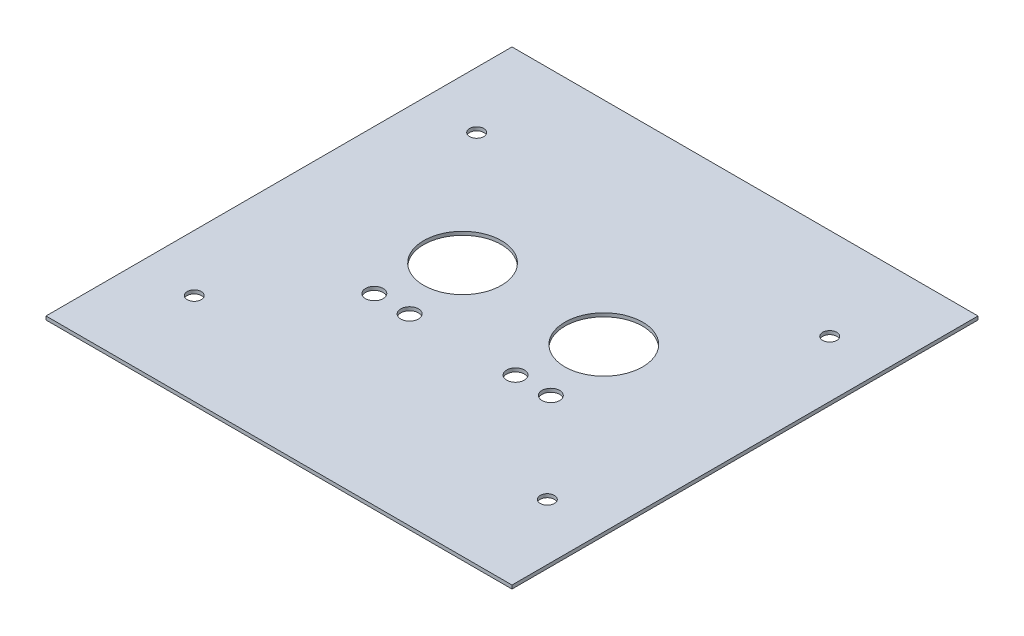
SolidWorks part; units mm, degrees
ref_plane "Front Plane" through (0, 0, 0) normal (0, 0, 1) x (1, 0, 0)
ref_plane "Top Plane" through (0, 0, 0) normal (0, 1, 0) x (1, 0, 0)
ref_plane "Right Plane" through (0, 0, 0) normal (1, 0, 0) x (0, 0, -1)
sketch "Sketch1" plane through (0, 0, 0) normal (0, 1, 0) x (1, 0, 0)
  line L1 (-26.6885, 109.7951) -> (105.3115, 109.7951)
  line L2 (-26.6885, 109.7951) -> (-26.6885, -22.2049)
  line L3 (-26.6885, -22.2049) -> (105.3115, -22.2049)
  line L4 (105.3115, 109.7951) -> (105.3115, -22.2049)
  circle A0 centre (14.3115, 29.7951) radius 2.5
  circle A1 centre (24.3115, 29.7951) radius 2.5
  circle A2 centre (54.3115, 29.7951) radius 2.5
  circle A3 centre (64.3115, 29.7951) radius 2.5
  circle A4 centre (19.3115, 49.7951) radius 11
  circle A5 centre (59.3115, 49.7951) radius 11
  dimension "D3" = 5
  dimension "D6" = 22
  dimension "D1" = 132
  dimension "D2" = 132
  dimension "D4" = 10
  dimension "D5" = 10
  dimension "D7" = 20
  dimension "D8" = 20
  dimension "D9" = 5
  dimension "D10" = 5
  dimension "D12" = 46
  dimension "D13" = 60
  dimension "D14" = 60
extrude "Boss-Extrude1" add sketch "Sketch1" along normal blind 1
sketch "Sketch2" plane through (0, 0, 0) normal (0, -1, 0) x (1, 0, 0)
  circle A0 centre (-10.6885, -3.7951) radius 2
  circle A1 centre (89.3115, -3.7951) radius 2
  circle A2 centre (89.3115, -83.7951) radius 2
  circle A3 centre (-10.6885, -83.7951) radius 2
  dimension "D1" = 4
  dimension "D2" = 4
  dimension "D3" = 4
  dimension "D4" = 4
extrude "Cut-Extrude1" cut sketch "Sketch2" against normal through all
